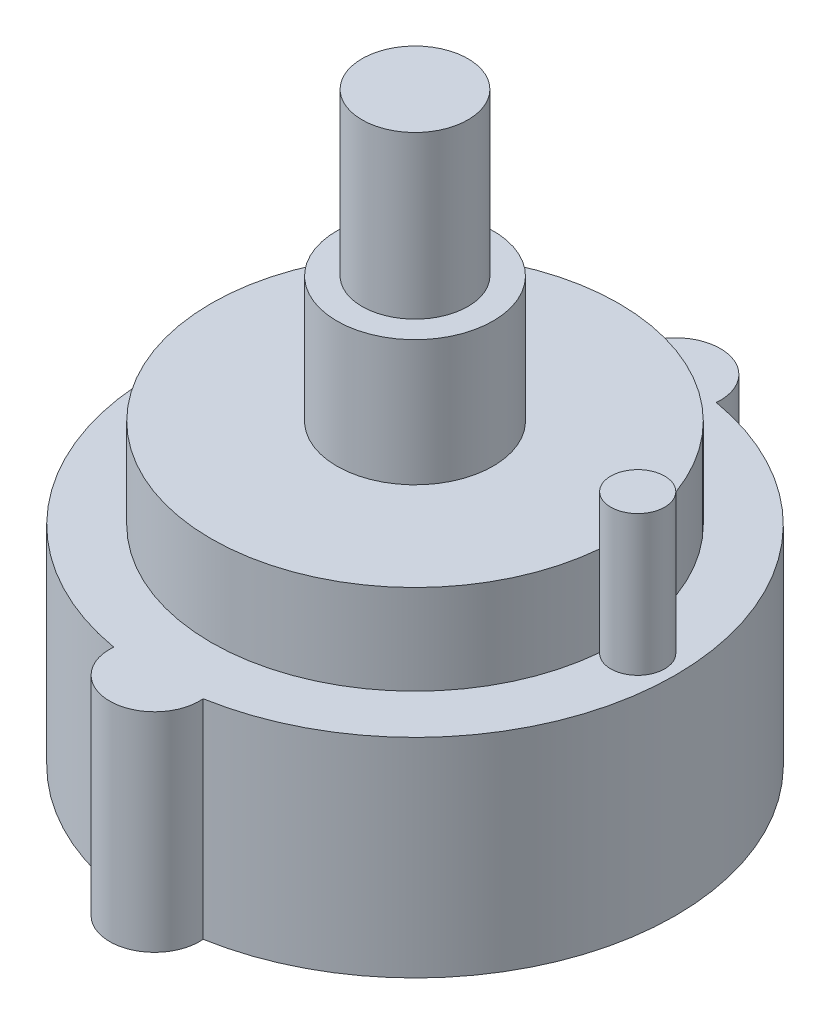
SolidWorks part; units mm, degrees
ref_plane "Спереди" through (0, 0, 0) normal (0, 0, 1) x (1, 0, 0)
ref_plane "Сверху" through (0, 0, 0) normal (0, 1, 0) x (1, 0, 0)
ref_plane "Справа" through (0, 0, 0) normal (1, 0, 0) x (0, 0, -1)
sketch "Sketch1" plane through (0, 0, 0) normal (0, 1, 0) x (1, 0, 0)
  circle A0 centre (0, 0) radius 14.5
  dimension "D1" = 29
extrude "Boss-Extrude1" add sketch "Sketch1" along normal blind 11.6
sketch "Sketch2" plane through (0, 11.6, 0) normal (0, 1, 0) x (1, 0, 0)
  circle A0 centre (0, 0) radius 11.35
  dimension "D1" = 22.7
extrude "Boss-Extrude2" add sketch "Sketch2" along normal blind 5
sketch "Sketch3" plane through (0, 16.6, 0) normal (0, 1, 0) x (1, 0, 0)
  circle A0 centre (0, 0) radius 4.35
  dimension "D1" = 8.7
extrude "Boss-Extrude3" add sketch "Sketch3" along normal blind 7
sketch "Sketch4" plane through (0, 23.6, 0) normal (0, 1, 0) x (1, 0, 0)
  circle A0 centre (0, 0) radius 2.95
  dimension "D1" = 5.9
extrude "Boss-Extrude4" add sketch "Sketch4" along normal blind 9
sketch "Sketch5" plane through (0, 0, 0) normal (0, -1, 0) x (1, 0, 0)
  line L0 (0, -14.5) -> (0, 14.5) construction
  circle A0 centre (0, 0) radius 14.5 construction
  circle A1 centre (0, 14.5) radius 2.5
  circle A2 centre (0, -14.5) radius 2.5
  point P7 (0, 0)
  dimension "D1" = 5
extrude "Boss-Extrude5" add sketch "Sketch5" against normal up to surface (11.6 mm away) up to face at (0, 11.6, 11.35)
sketch "Sketch6" plane through (0, 16.6, 0) normal (0, 1, 0) x (1, 0, 0)
  line L0 (0, 0) -> (12.4, 0) construction
  circle A0 centre (12.4, 0) radius 1.5
  dimension "D2" = 3
  dimension "D1" = 12.4
extrude "Boss-Extrude6" add sketch "Sketch6" along normal blind 2.8 and the other way up to surface (16.6 mm away)
